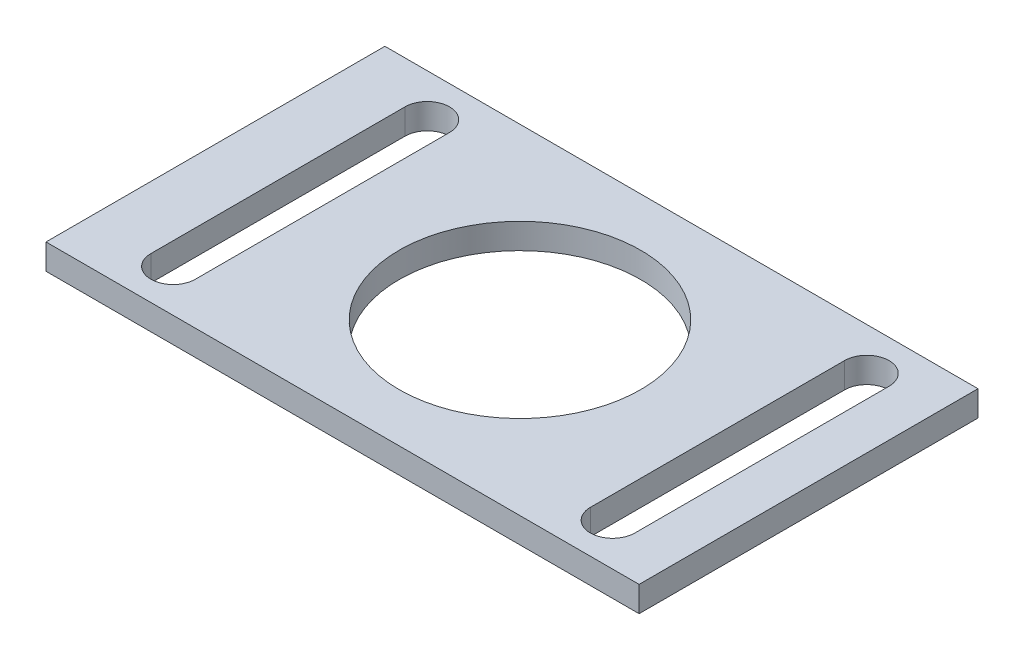
SolidWorks part; units mm, degrees
ref_plane "Front Plane" through (0, 0, 0) normal (0, 0, 1) x (1, 0, 0)
ref_plane "Top Plane" through (0, 0, 0) normal (0, 1, 0) x (1, 0, 0)
ref_plane "Right Plane" through (0, 0, 0) normal (1, 0, 0) x (0, 0, -1)
sketch "Sketch1" plane through (0, 0, 0) normal (0, 1, 0) x (1, 0, 0)
  line L1 (0, 0) -> (70, 0)
  line L2 (0, 0) -> (0, 40)
  line L3 (0, 40) -> (70, 40)
  line L4 (70, 0) -> (70, 40)
  dimension "D1" = 40
  dimension "7" = 70
extrude "Boss-Extrude1" add sketch "Sketch1" along normal blind 3 contours L3 L4 L1 L2
sketch "Sketch2" plane through (0, 3, 0) normal (0, 1, 0) x (1, 0, 0)
  line L0 (10, 35) -> (10, 5) construction
  line L1 (12.625, 35) -> (12.625, 5)
  line L2 (7.375, 35) -> (7.375, 5)
  line L3 (61.875, 35) -> (61.875, 5) construction
  line L4 (64.5, 35) -> (64.5, 5)
  line L5 (59.25, 35) -> (59.25, 5)
  line L7 (0, 20) -> (71.875, 20) construction
  line L8 (0, 0) -> (0, 40) construction
  circle A0 centre (35.9375, 20) radius 14.255
  arc A1 (12.625, 35) -> (7.375, 35) centre (10, 35) ccw
  arc A2 (7.375, 5) -> (12.625, 5) centre (10, 5) ccw
  arc A3 (64.5, 35) -> (59.25, 35) centre (61.875, 35) ccw
  arc A4 (59.25, 5) -> (64.5, 5) centre (61.875, 5) ccw
  point P4 (10, 20)
  point P9 (61.875, 20)
  point P16 (0, 0)
  point P17 (0, 0)
  point P22 (0, 20)
  point P23 (0, 0)
  point P24 (0, 0)
  dimension "D1" = 28.51
  dimension "D2" = 5.25
  dimension "D3" = 5.25
  dimension "D4" = 10
  dimension "D5" = 10
  dimension "D6" = 30
  dimension "D7" = 30
extrude "Cut-Extrude1" cut sketch "Sketch2" against normal blind 3
